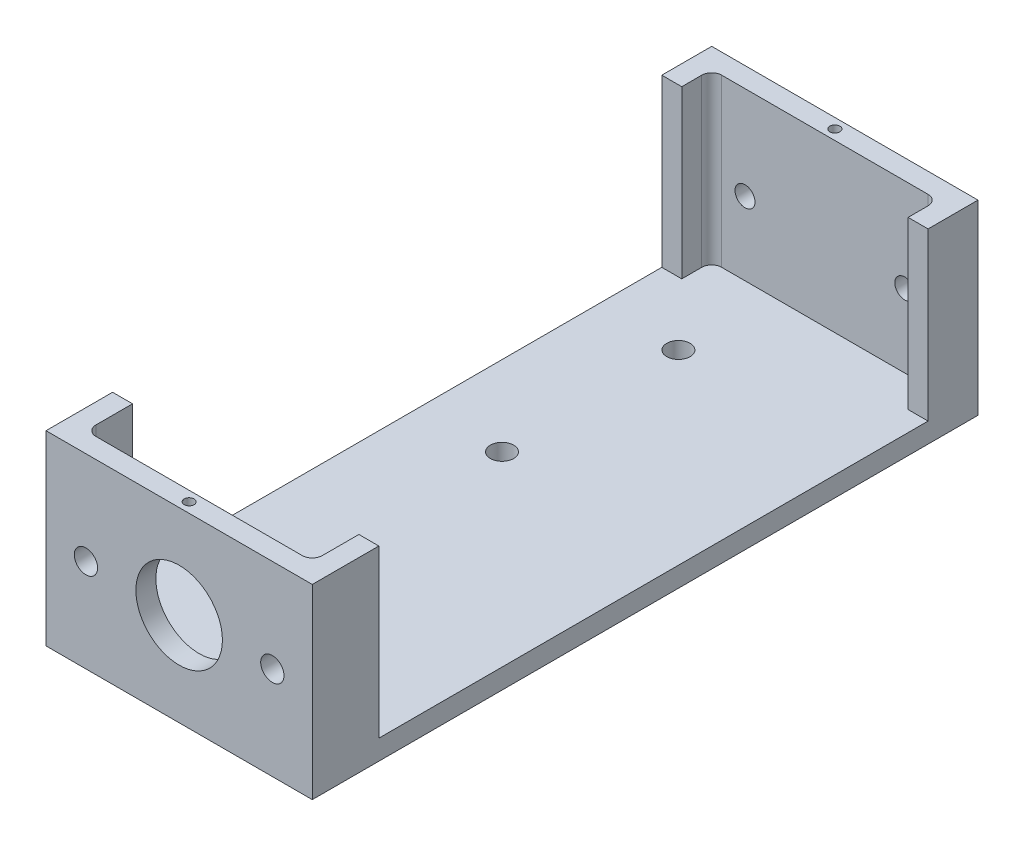
SolidWorks part; units mm, degrees
ref_plane "前视基准面" through (0, 0, 0) normal (0, 0, 1) x (1, 0, 0)
ref_plane "上视基准面" through (0, 0, 0) normal (0, 1, 0) x (1, 0, 0)
ref_plane "右视基准面" through (0, 0, 0) normal (1, 0, 0) x (0, 0, -1)
sketch "草图1" plane through (0, 0, 0) normal (0, 0, 1) x (1, 0, 0)
  line L1 (-40, -28) -> (40, -28)
  line L2 (-40, -28) -> (-40, 28)
  line L3 (-40, 28) -> (40, 28)
  line L4 (40, -28) -> (40, 28)
  line L5 (-40, -28) -> (40, 28) construction
  line L6 (-40, 28) -> (40, -28) construction
  point P0 (0, 0)
  dimension "D1" = 80
  dimension "D2" = 56
extrude "凸台-拉伸1" add sketch "草图1" against normal blind 200
sketch "草图2" plane through (0, 28, 0) normal (0, 1, 0) x (1, 0, 0)
  line L0 (-34, 191) -> (-34, 9)
  line L1 (-31, 6) -> (31, 6)
  line L2 (34, 9) -> (34, 191)
  line L3 (31, 194) -> (-31, 194)
  line L4 (-40, 0) -> (40, 0)
  line L5 (40, 0) -> (40, 200)
  line L6 (40, 200) -> (-40, 200)
  line L7 (-40, 200) -> (-40, 0)
  line L8 (-40, 0) -> (40, 0)
  line L9 (40, 0) -> (40, 200)
  line L10 (40, 200) -> (-40, 200)
  line L11 (-40, 200) -> (-40, 0)
  line L12 (-34, 6) -> (34, 6) construction
  line L13 (34, 6) -> (34, 194) construction
  line L14 (-34, 194) -> (-34, 6) construction
  line L15 (34, 194) -> (-34, 194) construction
  arc A0 (31, 6) -> (34, 9) centre (31, 9) ccw
  arc A1 (-34, 9) -> (-31, 6) centre (-31, 9) ccw
  arc A2 (34, 191) -> (31, 194) centre (31, 191) ccw
  arc A3 (-34, 191) -> (-31, 194) centre (-31, 191) cw
  dimension "D3" = 3
  dimension "D1" = 0
  dimension "D2" = 6
extrude "切除-拉伸1" cut sketch "草图2" against normal blind 50 contours A3 L0 A1 L1 A0 L2 A2 L3
sketch "草图3" plane through (0, 0, 0) normal (0, 0, 1) x (1, 0, 0)
  line L0 (0, 0) -> (0, 37.0041) construction
  line L1 (-40, -22) -> (40, -22) construction
  line L2 (-40, 28) -> (-40, -28) construction
  line L3 (40, -28) -> (40, 28) construction
  line L4 (-40, -28) -> (40, -28) construction
  line L5 (40, 28) -> (-40, 28) construction
  line L6 (-34, -22) -> (40, -22) construction
  line L9 (0, 0) -> (0, 28) construction
  line L10 (-28, 0) -> (28, 0) construction
  circle A0 centre (-28, 0) radius 3.5
  circle A1 centre (0, 0) radius 13
  circle A2 centre (28, 0) radius 3.5
  dimension "D2" = 7
  dimension "D3" = 26
  dimension "D4" = 7
  dimension "D1" = 6
  dimension "D5" = 28
  dimension "D6" = 28
  dimension "D7" = 28
extrude "切除-拉伸2" cut sketch "草图3" against normal blind 10
sketch "草图4" plane through (-40, 0, 0) normal (-1, 0, 0) x (0, 0, 1)
  line L0 (-126.5, -11) -> (-153.5, -11)
  line L1 (-126.5, -11) -> (-126.5, 25)
  line L2 (-126.5, 25) -> (-153.5, 25)
  line L3 (-153.5, -11) -> (-153.5, 25)
  line L4 (-140, -1.9135) -> (-140, 22.4271) construction
  line L5 (-200, 28) -> (0, 28) construction
  line L6 (-200, 28) -> (-200, -28) construction
  circle A0 centre (-121.5, -5) radius 2
  circle A1 centre (-121.5, 19) radius 2
  circle A2 centre (-158.5, 19) radius 2
  circle A3 centre (-158.5, -5) radius 2
  dimension "D1" = 4
  dimension "D2" = 4
  dimension "D3" = 36
  dimension "D4" = 6
  dimension "D5" = 5
  dimension "D6" = 6
  dimension "D7" = 5
  dimension "D8" = 27
  dimension "D9" = 3
  dimension "D10" = 60
extrude "切除-拉伸3" cut sketch "草图4" against normal blind 10
sketch "草图5" plane through (0, 0, -200) normal (0, 0, -1) x (-1, 0, 0)
  line L0 (0, -25.8214) -> (0, 19.1786) construction
  line L1 (0, 28) -> (0, 39.9128) construction
  line L2 (0, 0) -> (24, 0) construction
  line L5 (-40, 28) -> (40, 28) construction
  circle A0 centre (0, 0) radius 8 construction
  circle A1 centre (24, 0) radius 3
  circle A2 centre (-24, 0) radius 3
  dimension "D1" = 16
  dimension "D3" = 6
  dimension "D2" = 28
  dimension "D4" = 24
extrude "切除-拉伸4" cut sketch "草图5" against normal blind 10
sketch "草图6" plane through (0, -22, 0) normal (0, 1, 0) x (1, 0, 0)
  line L0 (-16, 113) -> (-16, 166) construction
  line L1 (-16, 139.5) -> (-23.7867, 139.5) construction
  line L2 (-34, 191) -> (-34, 9) construction
  line L3 (31, 194) -> (-31, 194) construction
  circle A0 centre (-16, 166) radius 3.5
  circle A1 centre (-16, 113) radius 3.5
  dimension "D2" = 7
  dimension "D5" = 7
  dimension "D1" = 53
  dimension "D3" = 18
  dimension "D4" = 54.5
extrude "切除-拉伸5" cut sketch "草图6" against normal blind 10
sketch "草图7" plane through (0, 28, 0) normal (0, 1, 0) x (1, 0, 0)
  line L0 (0, -10.1016) -> (0, 210.5413) construction
  line L1 (40, 0) -> (-40, 0) construction
  line L2 (40, 200) -> (40, 0) construction
  line L3 (-40, 200) -> (-40, 0) construction
  line L4 (40, 200) -> (-40, 200) construction
  circle A0 centre (-37, 150) radius 1.5
  circle A1 centre (-37, 50) radius 1.5
  circle A2 centre (37, 50) radius 1.5
  circle A3 centre (37, 150) radius 1.5
  circle A4 centre (0, 197) radius 1.5
  circle A5 centre (0, 3) radius 1.5
  dimension "D1" = 100
  dimension "D3" = 50
  dimension "D5" = 3
  dimension "D6" = 3
  dimension "D7" = 3
  dimension "D8" = 3
  dimension "D9" = 3
  dimension "D10" = 3
  dimension "D11" = 3
  dimension "D12" = 3
  dimension "D14" = 3
  dimension "D15" = 3
  dimension "D16" = 3
  dimension "D2" = 100
  dimension "D4" = 50
  dimension "D13" = 3
extrude "切除-拉伸6" cut sketch "草图7" against normal blind 10
sketch "草图8" plane through (40, 0, 0) normal (1, 0, 0) x (0, 0, -1)
  line L0 (200, 28) -> (0, 28) construction
  line L1 (20, 28) -> (185, 28)
  line L2 (20, 28) -> (20, -22)
  line L3 (20, -22) -> (185, -22)
  line L4 (185, 28) -> (185, -22)
  line L5 (20, 28) -> (185, -22) construction
  line L6 (20, -22) -> (185, 28) construction
  line L9 (0, -28) -> (0, 28) construction
  dimension "D1" = 165
  dimension "D2" = 50
  dimension "D3" = 20
extrude "切除-拉伸7" cut sketch "草图8" against normal through all
